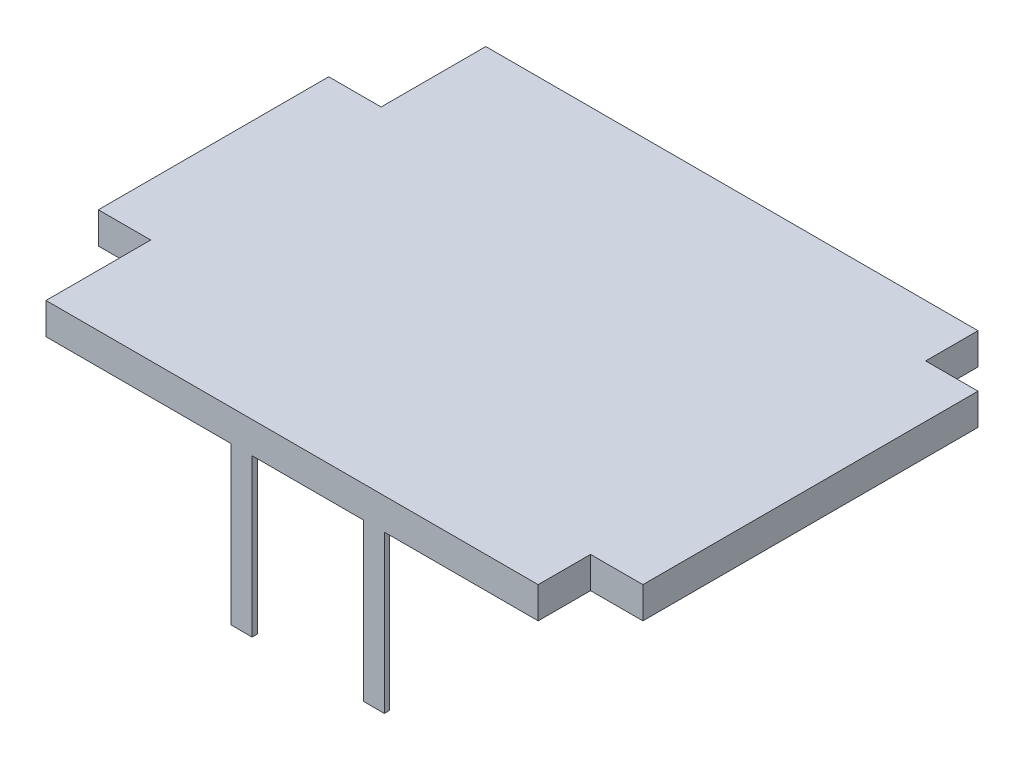
SolidWorks part; units mm, degrees
material "PBT (一般用)"
ref_plane "Front Plane" through (0, 0, 0) normal (0, 0, 1) x (1, 0, 0)
ref_plane "Top Plane" through (0, 0, 0) normal (0, 1, 0) x (1, 0, 0)
ref_plane "Right Plane" through (0, 0, 0) normal (1, 0, 0) x (0, 0, -1)
sketch "Sketch1" plane through (0, 0, 0) normal (0, 1, 0) x (1, 0, 0)
  line L0 (0, -1.1) -> (0.5, -1.1)
  line L1 (0.5, -0.1) -> (5.2, -0.1)
  line L2 (0, -1.1) -> (0, -3.3)
  line L3 (0.5, -4.3) -> (5.2, -4.3)
  line L4 (5.7, -0.6) -> (5.7, -3.8)
  line L5 (0.5, -1.1) -> (0.5, -0.1)
  line L6 (0, -3.3) -> (0.5, -3.3)
  line L7 (0.5, -3.3) -> (0.5, -4.3)
  line L11 (5.7, -3.8) -> (5.2, -3.8)
  line L12 (5.2, -4.3) -> (5.2, -3.8)
  line L15 (5.7, -0.6) -> (5.2, -0.6)
  line L16 (5.2, -0.1) -> (5.2, -0.6)
  dimension "D2" = 4.2
  dimension "D3" = 0.5
  dimension "D4" = 1
  dimension "D5" = 0.5
  dimension "D6" = 1
  dimension "D7" = 0.5
  dimension "D8" = 0.5
  dimension "D9" = 0.5
  dimension "D10" = 0.5
extrude "Boss-Extrude1" add sketch "Sketch1" along normal blind 0.3 contours L0 L5 L1 L16 L15 L4 L11 L12 L3 L7 L6 L2
sketch "Sketch2" plane through (0, 0, 0.1) normal (0, 0, -1) x (-1, 0, 0)
  line L0 (-0.5, 0) -> (-5.2, 0) construction
  line L1 (-3.731, 0) -> (-2.2679, 0)
  line L2 (-3.531, -1.5) -> (-3.531, -0.2)
  line L3 (-3.531, -1.5) -> (-3.731, -1.5)
  line L4 (-3.731, 0) -> (-3.731, -1.5)
  line L5 (-3.531, -0.2) -> (-2.4679, -0.2)
  line L11 (-2.2679, 0) -> (-2.2679, -1.5)
  line L12 (-2.2679, -1.5) -> (-2.4679, -1.5)
  line L13 (-2.4679, -0.2) -> (-2.4679, -1.5)
  dimension "D1" = 0.2
  dimension "D2" = 1.5
  dimension "D3" = 1.5
  dimension "D4" = 0.2
  dimension "D5" = 0.2
extrude "Boss-Extrude2" add sketch "Sketch2" against normal blind 0.05
sketch "Sketch4" plane through (0, 0, 0) normal (0, -1, 0) x (1, 0, 0)
  line L4 (0.5, 4.3) -> (5.2, 4.3) construction
  line L5 (2.4679, 4.25) -> (2.2679, 4.25)
  line L6 (2.4679, 4.25) -> (2.4679, 4.3)
  line L7 (2.4679, 4.3) -> (2.2679, 4.3)
  line L8 (2.2679, 4.25) -> (2.2679, 4.3)
  line L10 (3.531, 4.3) -> (3.731, 4.3)
  line L11 (3.531, 4.3) -> (3.531, 4.25)
  line L12 (3.531, 4.25) -> (3.731, 4.25)
  line L13 (3.731, 4.3) -> (3.731, 4.25)
  dimension "D1" = 0.05
  dimension "D2" = 0.05
extrude "Boss-Extrude3" add sketch "Sketch4" along normal blind 1.5
